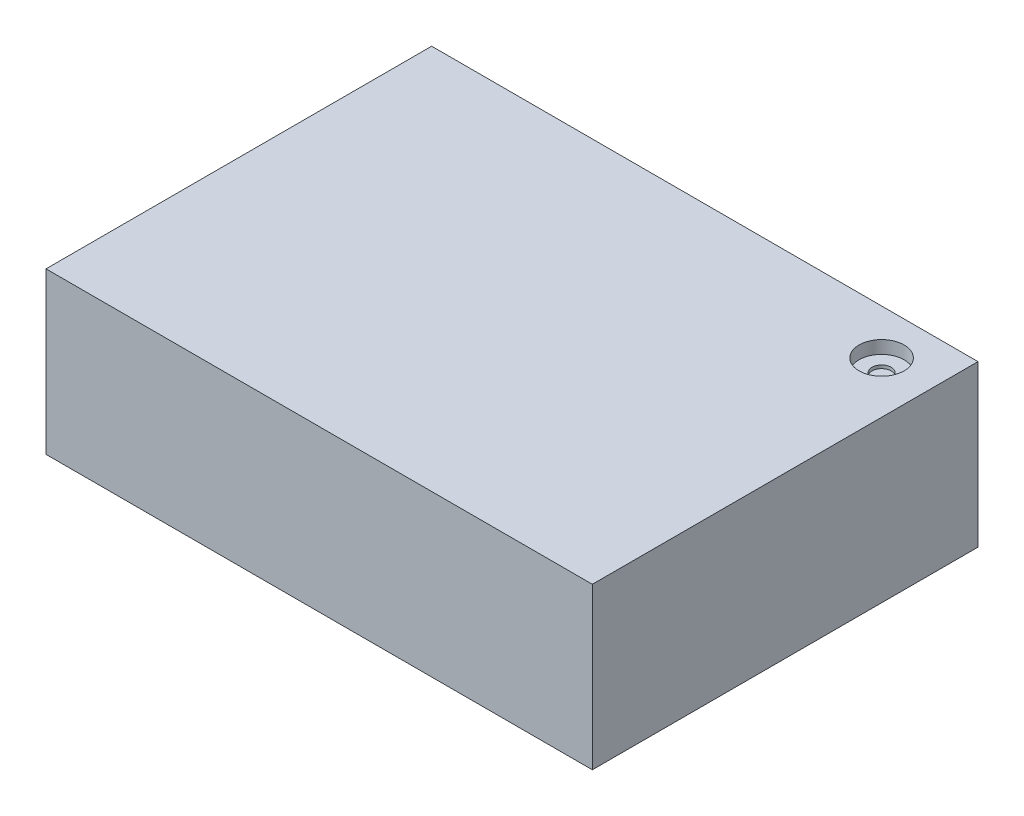
SolidWorks part; units mm, degrees
ref_plane "Front" through (0, 0, 0) normal (0, 0, 1) x (1, 0, 0)
ref_plane "Top" through (0, 0, 0) normal (0, 1, 0) x (1, 0, 0)
ref_plane "Right" through (0, 0, 0) normal (1, 0, 0) x (0, 0, -1)
sketch "Sketch1" plane through (0, 0, 0) normal (0, 1, 0) x (1, 0, 0)
  line L1 (-53.975, 38.1) -> (53.975, 38.1)
  line L2 (-53.975, 38.1) -> (-53.975, -38.1)
  line L3 (-53.975, -38.1) -> (53.975, -38.1)
  line L4 (53.975, 38.1) -> (53.975, -38.1)
  line L5 (-53.975, 38.1) -> (53.975, -38.1) construction
  line L6 (-53.975, -38.1) -> (53.975, 38.1) construction
  point P0 (0, 0)
  dimension "D1" = 76.2
  dimension "D2" = 107.95
extrude "Boss-Extrude1" add sketch "Sketch1" along normal blind 31.75
sketch "Sketch2" plane through (-53.975, 0, 0) normal (-1, 0, 0) x (0, 0, 1)
  line L0 (-38.1, 31.75) -> (-38.1, 0) construction
  line L1 (-38.1, 28.575) -> (34.925, 28.575)
  line L2 (-38.1, 28.575) -> (-38.1, 22.86)
  line L3 (-38.1, 22.86) -> (34.925, 22.86)
  line L4 (34.925, 28.575) -> (34.925, 22.86)
  line L5 (-38.1, 21.3783) -> (34.925, 21.3783)
  line L6 (-38.1, 15.6633) -> (34.925, 15.6633)
  line L7 (34.925, 21.3783) -> (34.925, 15.6633)
  line L8 (-38.1, 14.1817) -> (34.925, 14.1817)
  line L9 (-38.1, 8.4667) -> (34.925, 8.4667)
  line L10 (34.925, 14.1817) -> (34.925, 8.4667)
  line L11 (-38.1, 6.985) -> (34.925, 6.985)
  line L12 (-38.1, 1.27) -> (34.925, 1.27)
  line L13 (34.925, 6.985) -> (34.925, 1.27)
  line L14 (-38.1, 31.75) -> (38.1, 31.75) construction
  line L15 (-38.1, 21.3783) -> (-38.1, 15.6633)
  line L16 (-38.1, 14.1817) -> (-38.1, 8.4667)
  line L17 (-38.1, 6.985) -> (-38.1, 1.27)
  line L18 (-38.1, 0) -> (38.1, 0) construction
  line L19 (38.1, 31.75) -> (38.1, 0) construction
  dimension "D2" = 3.175
  dimension "D3" = 5.715
  dimension "D5" = 3.175
  dimension "D6" = 1.27
  dimension "D1" = 4
  dimension "D4" = 4
extrude "Cut-Extrude1" cut sketch "Sketch2" against normal offset from surface (104.775 mm away) 3.175 up to face at (53.975, 15.875, 0)
sketch "Sketch3" plane through (0, 31.75, 0) normal (0, 1, 0) x (1, 0, 0)
  line L0 (53.975, -38.1) -> (53.975, 38.1) construction
  line L1 (53.975, 38.1) -> (-53.975, 38.1) construction
  circle A0 centre (43.815, 29.21) radius 1.8923
  dimension "D1" = 3.7846
  dimension "D2" = 10.16
  dimension "D3" = 8.89
extrude "Cut-Extrude2" cut sketch "Sketch3" against normal through all
sketch "Sketch4" plane through (0, 31.75, 0) normal (0, 1, 0) x (1, 0, 0)
  circle A0 centre (43.815, 29.21) radius 4.445
  dimension "D1" = 8.89
extrude "Cut-Extrude3" cut sketch "Sketch4" against normal blind 2.54
